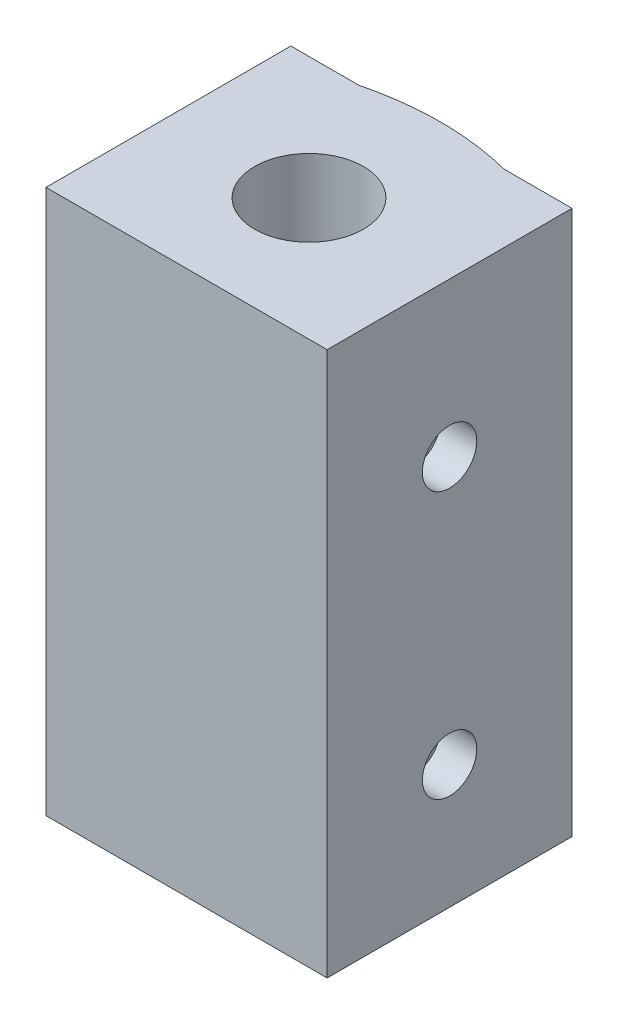
SolidWorks part; units mm, degrees
ref_plane "Front Plane" through (0, 0, 0) normal (0, 0, 1) x (1, 0, 0)
ref_plane "Top Plane" through (0, 0, 0) normal (0, 1, 0) x (1, 0, 0)
ref_plane "Right Plane" through (0, 0, 0) normal (1, 0, 0) x (0, 0, -1)
sketch "Sketch1" plane through (0, 0, 0) normal (0, 1, 0) x (1, 0, 0)
  line L0 (7.75, 0) -> (7.75, -2.25) construction
  line L1 (0, 0) -> (15.5, 0)
  line L2 (0, 0) -> (0, 13.5)
  line L3 (0, 13.5) -> (3.75, 13.5)
  line L4 (15.5, 0) -> (15.5, 13.5)
  line L5 (11.75, 13.5) -> (15.5, 13.5)
  arc A0 (3.75, 13.5) -> (11.75, 13.5) centre (7.75, -2.25) cw
  point P8 (7.75, 14)
  dimension "D1" = 15.5
  dimension "D2" = 13.5
  dimension "D3" = 14
  dimension "D4" = 8
extrude "Boss-Extrude1" add sketch "Sketch1" along normal blind 30
sketch "Sketch2" plane through (0, 30, 0) normal (0, 1, 0) x (1, 0, 0)
  line L0 (0, 6.75) -> (7.75, 6.75) construction
  line L1 (0, 13.5) -> (0, 0) construction
  line L2 (7.75, 0) -> (7.75, 6.75) construction
  line L3 (0, 0) -> (15.5, 0) construction
  circle A0 centre (7.75, 6.75) radius 3
  dimension "D1" = 6
extrude "Cut-Extrude1" cut sketch "Sketch2" against normal offset from surface (18 mm away) 18 up to face at (7.75, 30, -9.0833)
sketch "Sketch3" plane through (0, 12, 0) normal (0, 1, 0) x (1, 0, 0)
  circle A0 centre (7.75, 6.75) radius 1.75
  circle A1 centre (7.75, 6.75) radius 3 construction
  dimension "D1" = 3.5
extrude "Cut-Extrude2" cut sketch "Sketch3" against normal through all
sketch "Sketch4" plane through (15.5, 0, 0) normal (1, 0, 0) x (0, 0, -1)
  line L2 (6.75, 30) -> (6.75, 0) construction
  line L3 (0, 30) -> (13.5, 30) construction
  line L4 (0, 0) -> (13.5, 0) construction
  circle A0 centre (6.75, 21.515) radius 1.5
  circle A1 centre (6.75, 6.815) radius 1.5
  dimension "D1" = 3
  dimension "D2" = 6.815
  dimension "D3" = 14.7
extrude "Cut-Extrude3" cut sketch "Sketch4" against normal blind 2
